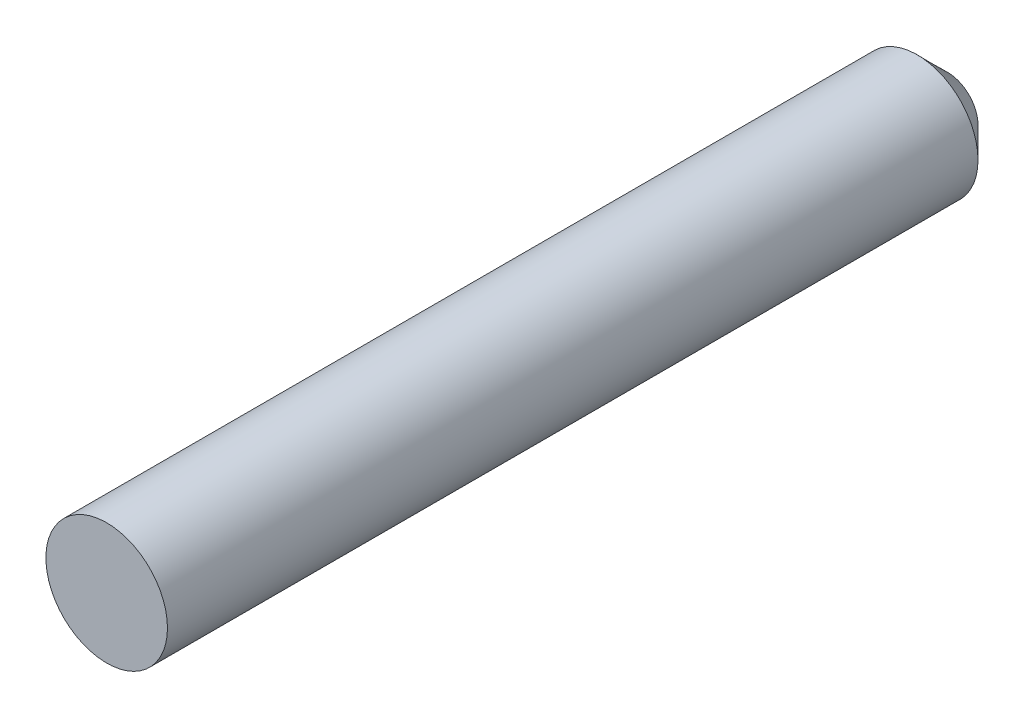
SolidWorks part; units mm, degrees
ref_plane "Front Plane" through (0, 0, 0) normal (0, 0, 1) x (1, 0, 0)
ref_plane "Top Plane" through (0, 0, 0) normal (0, 1, 0) x (1, 0, 0)
ref_plane "Right Plane" through (0, 0, 0) normal (1, 0, 0) x (0, 0, -1)
sketch "Sketch1" plane through (0, 0, 0) normal (0, 0, 1) x (1, 0, 0)
  circle A0 centre (0, 0) radius 6
  dimension "D1" = 12
extrude "Boss-Extrude1" add sketch "Sketch1" along normal blind 83
chamfer "Chamfer1" distance 3 angle 45 1 edges at (6, 0, 0)
